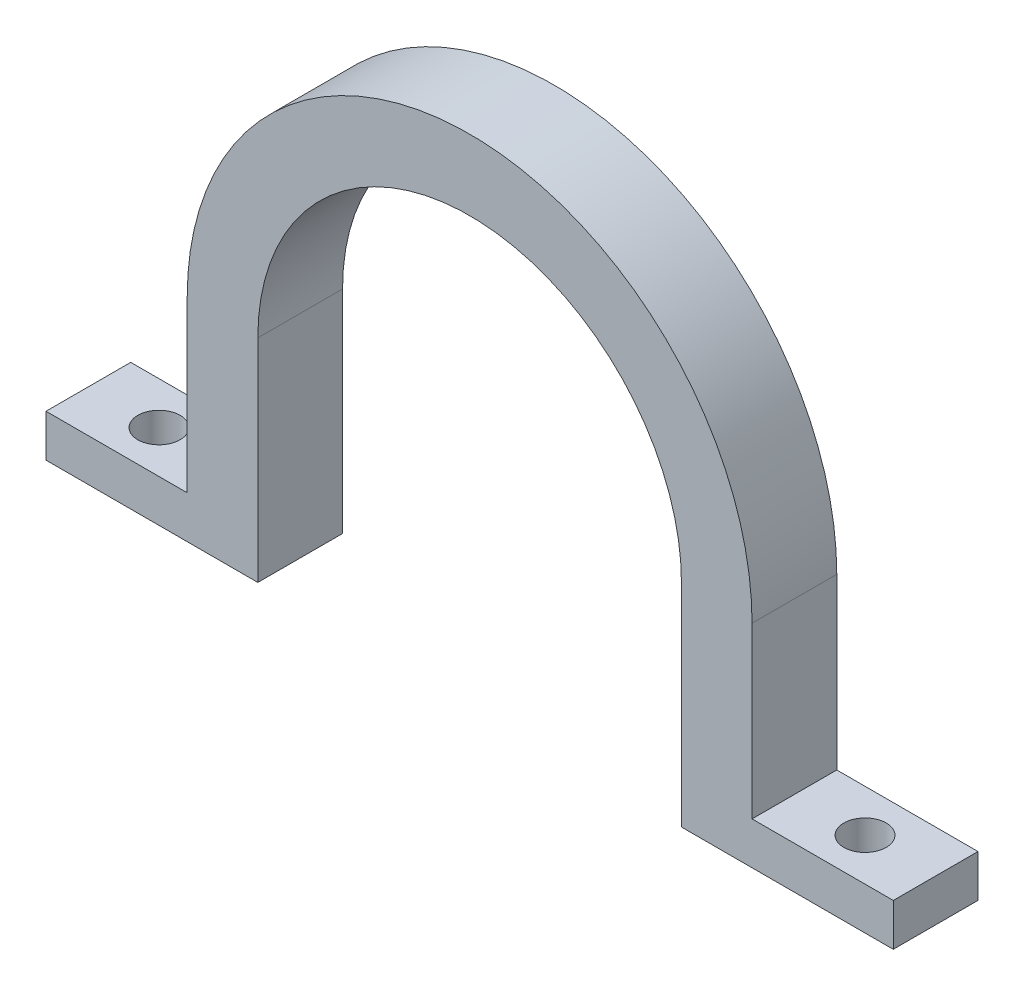
SolidWorks part; units mm, degrees
ref_plane "Front Plane" through (0, 0, 0) normal (0, 0, 1) x (1, 0, 0)
ref_plane "Top Plane" through (0, 0, 0) normal (0, 1, 0) x (1, 0, 0)
ref_plane "Right Plane" through (0, 0, 0) normal (1, 0, 0) x (0, 0, -1)
sketch "Sketch1" plane through (0, 0, 0) normal (0, 0, 1) x (1, 0, 0)
  line L0 (15, 0) -> (15, -15)
  line L1 (15, -15) -> (30, -15)
  line L2 (-30, -12) -> (-30, -15)
  line L3 (-15, -15) -> (-30, -15)
  line L4 (20, 0) -> (20, -12)
  line L6 (30, -12) -> (20, -12)
  line L8 (-30, -12) -> (-20, -12)
  line L9 (-20, 0) -> (-20, -12)
  line L10 (-15, 0) -> (-15, -15)
  line L11 (30, -12) -> (30, -15)
  arc A0 (15, 0) -> (-15, 0) centre (0, 0) ccw
  arc A1 (20, 0) -> (-20, 0) centre (0, 0) ccw
  point P7 (-30.1938, -12)
  point P9 (0, -15)
  point P17 (30, -11.7565)
extrude "Boss-Extrude1" add sketch "Sketch1" along normal blind 6 contours A0 L10 L3 L2 L8 L9 A1 L4 L6 L11 L1 L0
sketch "Sketch2" plane through (0, -12, 0) normal (0, 1, 0) x (1, 0, 0)
  circle A2 centre (-25, -3) radius 1.5
  circle A3 centre (25, -3) radius 1.5
extrude "Cut-Extrude1" cut sketch "Sketch2" against normal blind 3 contours A2 | A3
